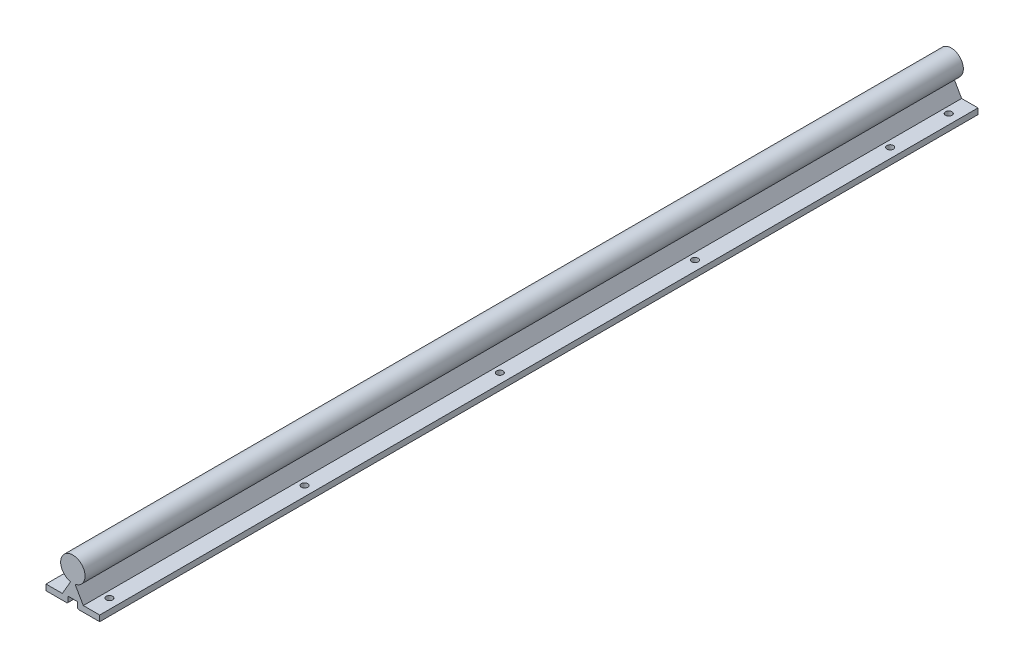
SolidWorks part; units mm, degrees
material "1060 Alloy"
ref_plane "Front Plane" through (0, 0, 0) normal (0, 0, 1) x (1, 0, 0)
ref_plane "Top Plane" through (0, 0, 0) normal (0, 1, 0) x (1, 0, 0)
ref_plane "Right Plane" through (0, 0, 0) normal (1, 0, 0) x (0, 0, -1)
sketch "Sketch1" plane through (0, 0, 0) normal (0, 0, 1) x (1, 0, 0)
  line L0 (-27.5, 0) -> (-4.75, 0)
  line L1 (10.75, 6) -> (2.0897, 21)
  line L2 (-4.75, 0) -> (-4.75, 6.5)
  line L3 (-4.75, 6.5) -> (4.75, 6.5)
  line L4 (-27.5, 0) -> (-27.5, 6)
  line L5 (-27.5, 6) -> (-10.75, 6)
  line L6 (-10.75, 6) -> (-2.0897, 21)
  line L7 (-2.0897, 21) -> (2.0897, 21)
  line L8 (0, 0) -> (0, 50.9475) construction
  line L9 (27.5, 6) -> (10.75, 6)
  line L10 (27.5, 0) -> (27.5, 6)
  line L11 (4.75, 0) -> (4.75, 6.5)
  line L12 (27.5, 0) -> (4.75, 0)
  circle A0 centre (0, 33) radius 12.5
  point P21 (0, 21)
  point P25 (0, 6.5)
  dimension "D1" = 55
  dimension "D5" = 25
  dimension "D2" = 21
  dimension "D3" = 6
  dimension "D4" = 6.5
  dimension "D6" = 21.5
  dimension "D7" = 9.5
  dimension "D8" = 30
  dimension "D9" = 33
extrude "Boss-Extrude1" add sketch "Sketch1" against normal blind 900 contours L7 L8 A0 L6 | L8 L7 L1 A0 | L8 L3 L11 L12 L10 L9 L1 A0 | L3 L8 A0 L6 L5 L4 L0 L2 | L8 A0 L1 L7 | A0 L8 L7 L6
chamfer "Chamfer1" distance 1 angle 45 2 edges at (-4.75, 0, -450) (4.75, 0, -450)
sketch "Sketch2" plane through (0, 6, 0) normal (0, 1, 0) x (1, 0, 0)
  line L0 (27.5, 0) -> (10.75, 0) construction
  line L1 (0, 0) -> (0, 13.9025) construction
  line L2 (27.5, 900) -> (10.75, 900) construction
  line L3 (0, 900) -> (0, 1839.438) construction
  line L4 (12.5, 900) -> (-12.5, 900) construction
  circle A0 centre (17.5, 20) radius 3.3
  circle A1 centre (-17.5, 20) radius 3.3
  circle A2 centre (-17.5, 220) radius 3.3
  circle A3 centre (17.5, 220) radius 3.3
  circle A4 centre (-17.5, 420) radius 3.3
  circle A5 centre (17.5, 420) radius 3.3
  circle A6 centre (-17.5, 620) radius 3.3
  circle A7 centre (17.5, 620) radius 3.3
  circle A8 centre (-17.5, 820) radius 3.3
  circle A9 centre (17.5, 820) radius 3.3
  circle A10 centre (-17.5, 1020) radius 3.3
  circle A11 centre (17.5, 1020) radius 3.3
  circle A12 centre (-17.5, 1220) radius 3.3
  circle A13 centre (17.5, 1220) radius 3.3
  circle A14 centre (-17.5, 1420) radius 3.3
  circle A15 centre (17.5, 1420) radius 3.3
  circle A16 centre (-17.5, 1620) radius 3.3
  circle A17 centre (17.5, 1620) radius 3.3
  circle A20 centre (17.5, 880) radius 3.3
  circle A21 centre (-17.5, 880) radius 3.3
  point P53 (0, 900)
  dimension "D1" = 6.6
  dimension "D6" = 6.6
  dimension "D2" = 20
  dimension "D3" = 35
  dimension "D5" = 200
  dimension "D7" = 20
  dimension "D4" = 9
extrude "Cut-Extrude1" cut sketch "Sketch2" against normal through all both and the other way through all
